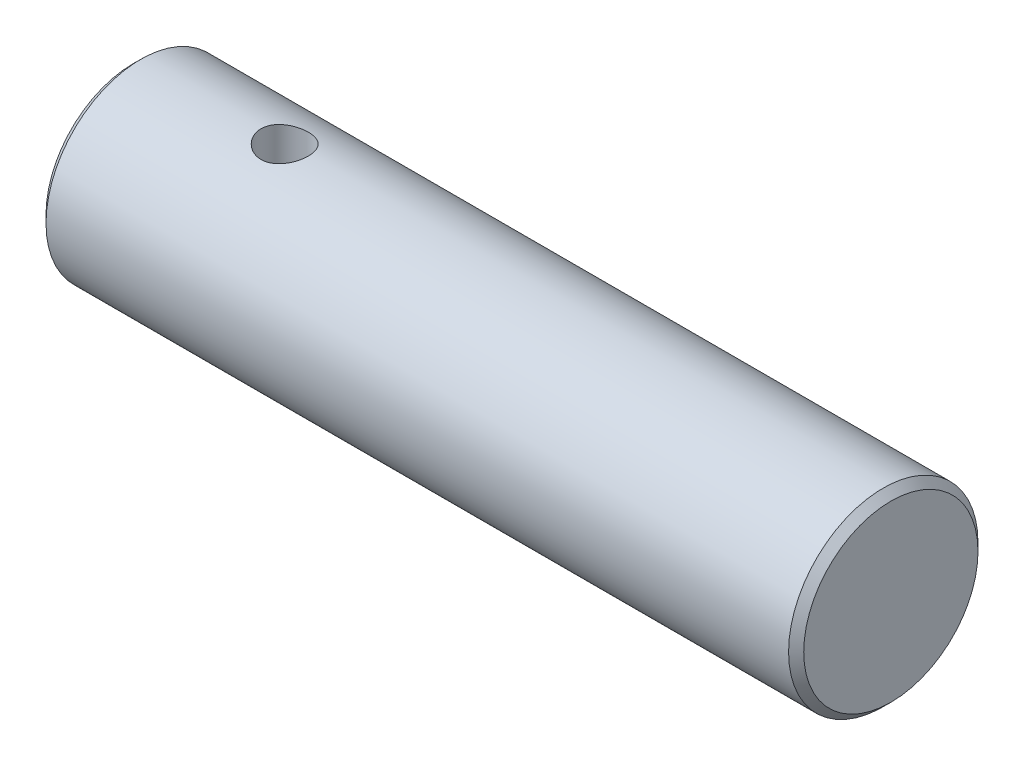
SolidWorks part; units mm, degrees
material "6061 Alloy"
ref_plane "Front Plane" through (0, 0, 0) normal (0, 0, 1) x (1, 0, 0)
ref_plane "Top Plane" through (0, 0, 0) normal (0, 1, 0) x (1, 0, 0)
ref_plane "Right Plane" through (0, 0, 0) normal (1, 0, 0) x (0, 0, -1)
sketch "Sketch2" plane through (0, 0, 0) normal (1, 0, 0) x (0, 0, -1)
  circle A0 centre (0, 0) radius 3.175
  dimension "D1" = 6.35
extrude "Boss-Extrude1" add sketch "Sketch2" along normal blind 25.4
chamfer "Chamfer1" distance 0.254 angle 45 2 edges at (25.4, 0, -3.175) (0, 0, -3.175)
sketch "Sketch4" plane through (0, 0, 0) normal (0, 1, 0) x (1, 0, 0)
  circle A0 centre (5.08, 0) radius 0.7938
  dimension "D1" = 1.5875
  dimension "D2" = 5.08
extrude "Cut-Extrude2" cut sketch "Sketch4" against normal through all both and the other way through all
